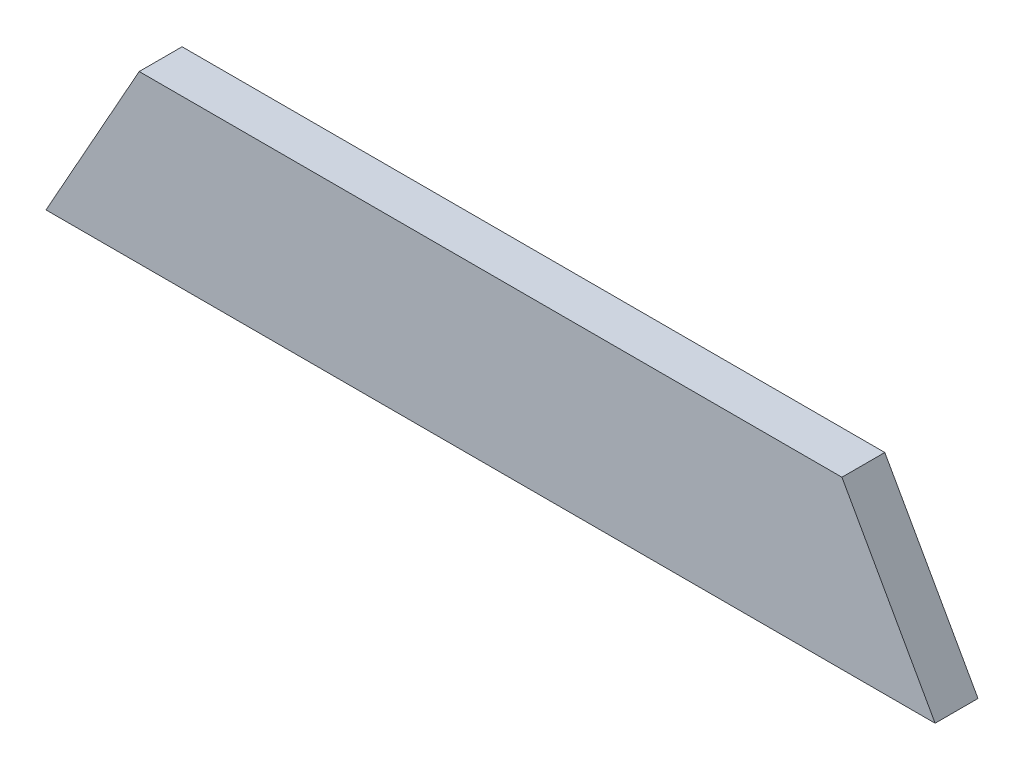
SolidWorks part; units mm, degrees
ref_plane "Front Plane" through (0, 0, 0) normal (0, 0, 1) x (1, 0, 0)
ref_plane "Top Plane" through (0, 0, 0) normal (0, 1, 0) x (1, 0, 0)
ref_plane "Right Plane" through (0, 0, 0) normal (1, 0, 0) x (0, 0, -1)
sketch "Sketch1" plane through (0, 0, 0) normal (0, 0, 1) x (1, 0, 0)
  line L0 (0, 0) -> (75.4, 0)
  line L1 (-10, -17.8612) -> (85.4, -17.8612)
  line L2 (0, 0) -> (-10, -17.8612)
  line L3 (75.4, 0) -> (85.4, -17.8612)
  dimension "D1" = 75.4
  dimension "D2" = 95.4
  dimension "D3" = 20.47
  dimension "D4" = 20.47
extrude "Boss-Extrude1" add sketch "Sketch1" along normal blind 4.6
equation "\"D1@Boss-Extrude1\"=\"mat@levv1.assembly\""
